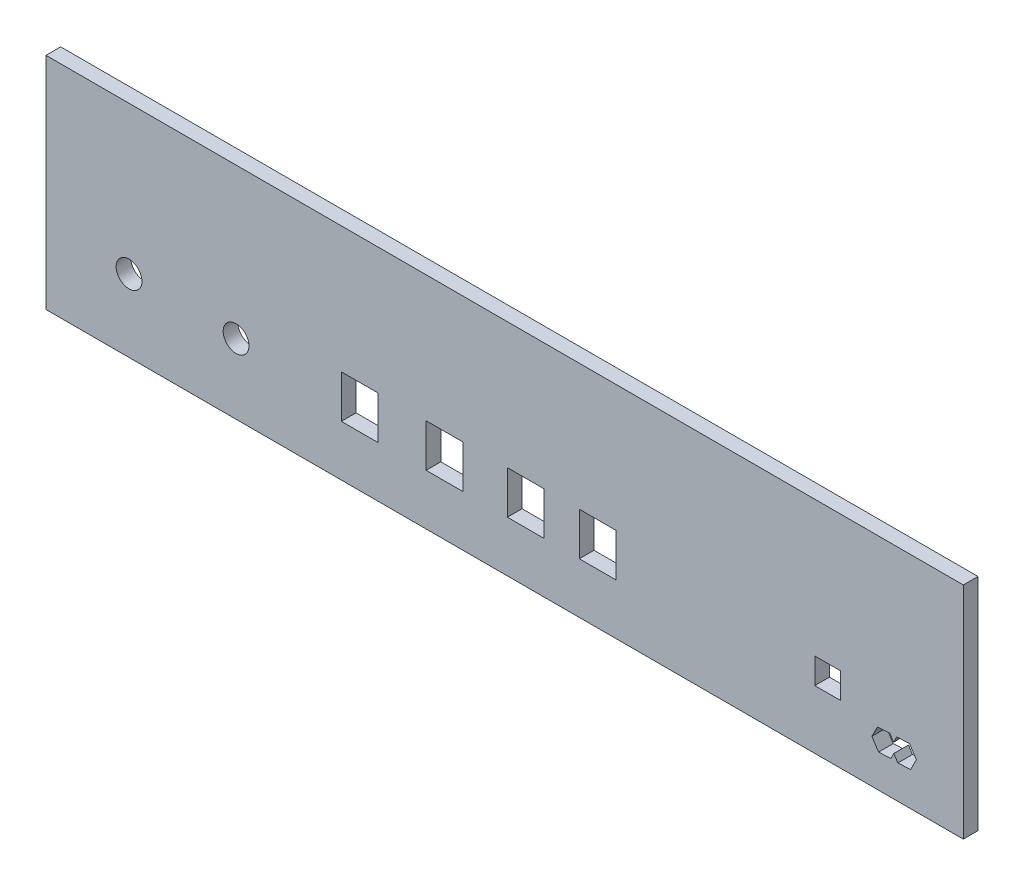
SolidWorks part; units mm, degrees
material "Balsa"
ref_plane "Front Plane" through (0, 0, 0) normal (0, 0, 1) x (1, 0, 0)
ref_plane "Top Plane" through (0, 0, 0) normal (0, 1, 0) x (1, 0, 0)
ref_plane "Right Plane" through (0, 0, 0) normal (1, 0, 0) x (0, 0, -1)
sketch "Sketch1" plane through (0, 0, 0) normal (0, 0, 1) x (1, 0, 0)
  line L1 (-112.4302, 80.4492) -> (137.5698, 80.4492)
  line L2 (-112.4302, 80.4492) -> (-112.4302, 20.4492)
  line L3 (-112.4302, 20.4492) -> (137.5698, 20.4492)
  line L4 (137.5698, 80.4492) -> (137.5698, 20.4492)
  dimension "D1" = 250
  dimension "D2" = 60
extrude "Boss-Extrude1" add sketch "Sketch1" along normal blind 4
sketch "Sketch3" plane through (0, 0, 4) normal (0, 0, 1) x (1, 0, 0)
  circle A0 centre (-89.7983, 40.153) radius 3.5189
  circle A1 centre (-117.3221, -107.101) radius 3.5189
  circle A2 centre (-60.6253, 39.4929) radius 3.5189
extrude "Cut-Extrude1" cut sketch "Sketch3" against normal blind 10
sketch "Sketch4" plane through (0, 0, 4) normal (0, 0, 1) x (1, 0, 0)
  line L0 (-8.8327, 46.0023) -> (1.1673, 46.0023)
  line L1 (-31.9446, 46.0023) -> (-21.9446, 46.0023)
  line L2 (-31.9446, 46.0023) -> (-31.9446, 34.3023)
  line L3 (-31.9446, 34.3023) -> (-21.9446, 34.3023)
  line L4 (-21.9446, 46.0023) -> (-21.9446, 34.3023)
  line L5 (-8.8327, 46.0023) -> (-8.8327, 34.3023)
  line L6 (-8.8327, 34.3023) -> (1.1673, 34.3023)
  line L7 (1.1673, 46.0023) -> (1.1673, 34.3023)
  line L12 (32.9141, 46.0023) -> (42.9141, 46.0023)
  line L13 (32.9141, 46.0023) -> (32.9141, 34.3023)
  line L14 (32.9141, 34.3023) -> (42.9141, 34.3023)
  line L15 (42.9141, 46.0023) -> (42.9141, 34.3023)
  line L16 (13.3066, 46.0023) -> (23.3066, 46.0023)
  line L17 (13.3066, 46.0023) -> (13.3066, 34.3023)
  line L18 (13.3066, 34.3023) -> (23.3066, 34.3023)
  line L19 (23.3066, 46.0023) -> (23.3066, 34.3023)
  dimension "D1" = 10
  dimension "D2" = 11.7
extrude "Cut-Extrude2" cut sketch "Sketch4" against normal blind 10
sketch "Sketch5" plane through (0, 0, 4) normal (0, 0, 1) x (1, 0, 0)
  line L1 (97.0875, 43.4455) -> (104.0875, 43.4455)
  line L2 (97.0875, 43.4455) -> (97.0875, 36.4455)
  line L3 (97.0875, 36.4455) -> (104.0875, 36.4455)
  line L4 (104.0875, 43.4455) -> (104.0875, 36.4455)
  dimension "D1" = 7
  dimension "D2" = 7
extrude "Cut-Extrude3" cut sketch "Sketch5" against normal blind 10
sketch "Sketch6" plane through (0, 0, 4) normal (0, 0, 1) x (1, 0, 0)
  line L1 (117.5256, 35.4201) -> (114.1749, 35.2516)
  line L2 (114.1749, 35.2516) -> (112.6455, 32.2656)
  line L3 (112.6455, 32.2656) -> (114.4668, 29.4481)
  line L4 (114.4668, 29.4481) -> (117.8174, 29.6166)
  line L5 (117.8174, 29.6166) -> (119.3468, 32.6026)
  line L6 (119.3468, 32.6026) -> (117.5256, 35.4201)
  line L7 (124.7772, 32.7768) -> (122.8941, 35.69)
  line L8 (122.8941, 35.69) -> (119.4296, 35.5158)
  line L9 (119.4296, 35.5158) -> (117.8482, 32.4283)
  line L10 (117.8482, 32.4283) -> (119.7313, 29.5151)
  line L11 (119.7313, 29.5151) -> (123.1958, 29.6893)
  line L12 (123.1958, 29.6893) -> (124.7772, 32.7768)
  circle A0 centre (115.9962, 32.4341) radius 2.9054 construction
  circle A1 centre (121.3127, 32.6026) radius 3.0041 construction
extrude "Cut-Extrude4" cut sketch "Sketch6" against normal blind 10 contours L10 L9 L6 L1 L2 L3 L4 L5 | L11 L12 L7 L8 L9 L6 L5 L10 | L9 L10 L5 L6
